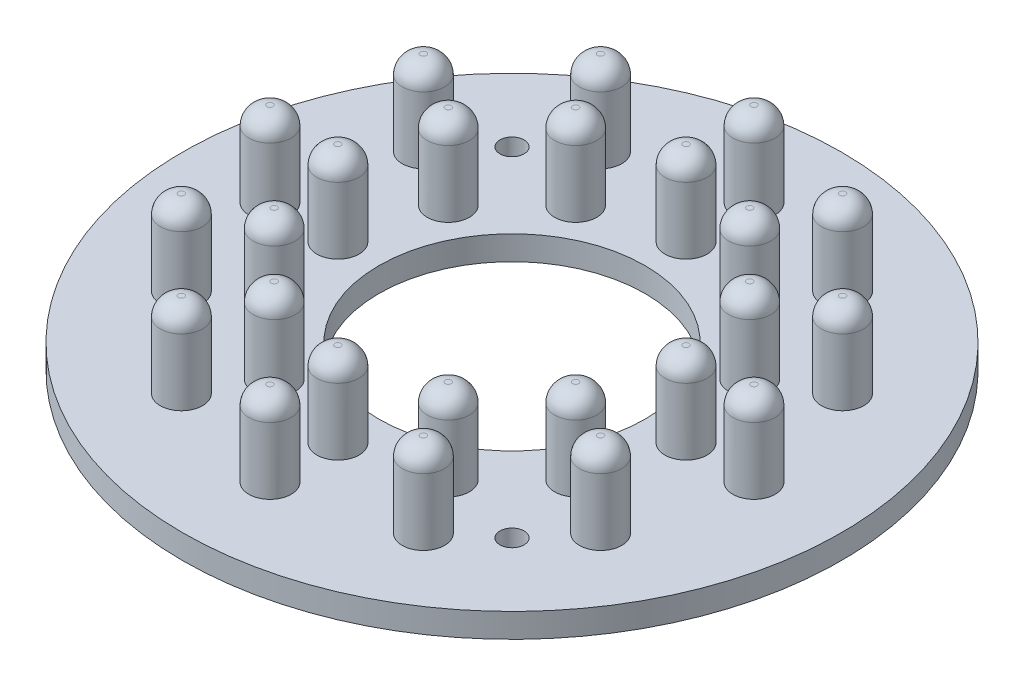
SolidWorks part; units mm, degrees
ref_plane "Front Plane" through (0, 0, 0) normal (0, 0, 1) x (1, 0, 0)
ref_plane "Top Plane" through (0, 0, 0) normal (0, 1, 0) x (1, 0, 0)
ref_plane "Right Plane" through (0, 0, 0) normal (1, 0, 0) x (0, 0, -1)
sketch "Sketch1" plane through (0, 0, 0) normal (0, 1, 0) x (1, 0, 0)
  circle A0 centre (0, 0) radius 11
  circle A1 centre (0, 0) radius 27.25
  dimension "D1" = 54.5
  dimension "D2" = 22
extrude "Boss-Extrude1" add sketch "Sketch1" along normal blind 2
sketch "Sketch2" plane through (0, 2, 0) normal (0, 1, 0) x (1, 0, 0)
  circle A0 centre (0, 14.3913) radius 1.75
  circle A1 centre (0, 20.0103) radius 1.75
  dimension "D1" = 3.5
extrude "Boss-Extrude2" add sketch "Sketch2" along normal blind 7
sketch "Sketch3" plane through (0, 2, 0) normal (0, 1, 0) x (1, 0, 0)
  line L0 (0, 0) -> (-14.0007, 14.0007) construction
  line L1 (0, 0) -> (0, 6.8686) construction
  circle A0 centre (-14.0007, 14.0007) radius 1
  dimension "D3" = 2
  dimension "D1" = 45
  dimension "D2" = 19.8
extrude "Cut-Extrude1" cut sketch "Sketch3" against normal through all
pattern_circular "CirPattern1" count 4 over 360 about axis through (0, 0, 0) along (0, 1, 0) of "Cut-Extrude1"
fillet "Fillet1" radius 1.5 2 edges at (0, 9, -12.6413) (0, 9, -18.2603)
pattern_circular "CirPattern2" count 12 over 360 about axis through (0, 0, 0) along (0, 1, 0) of "Boss-Extrude2", "Fillet1"
